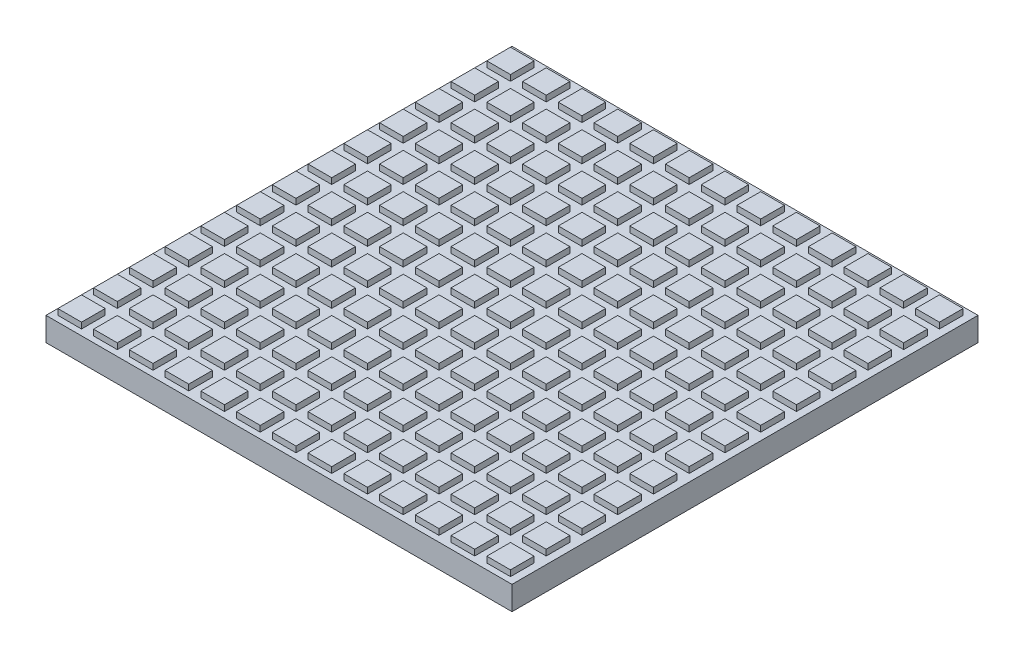
SolidWorks part; units mm, degrees
ref_plane "Front Plane" through (0, 0, 0) normal (0, 0, 1) x (1, 0, 0)
ref_plane "Top Plane" through (0, 0, 0) normal (0, 1, 0) x (1, 0, 0)
ref_plane "Right Plane" through (0, 0, 0) normal (1, 0, 0) x (0, 0, -1)
sketch "Sketch1" plane through (0, 0, 0) normal (0, 1, 0) x (1, 0, 0)
  line L1 (-250, -250) -> (250, -250)
  line L2 (-250, -250) -> (-250, 250)
  line L3 (-250, 250) -> (250, 250)
  line L4 (250, -250) -> (250, 250)
  line L5 (-250, -250) -> (250, 250) construction
  line L6 (-250, 250) -> (250, -250) construction
  point P0 (0, 0)
  dimension "D1" = 500
  dimension "D2" = 500
extrude "Boss-Extrude1" add sketch "Sketch1" along normal blind 25.4
sketch "Sketch2" plane through (0, 25.4, 0) normal (0, 1, 0) x (1, 0, 0)
  line L0 (-250, -250) -> (250, -250) construction
  line L1 (-243.65, -243.65) -> (-218.25, -243.65)
  line L2 (-243.65, -243.65) -> (-243.65, -218.25)
  line L3 (-243.65, -218.25) -> (-218.25, -218.25)
  line L4 (-218.25, -243.65) -> (-218.25, -218.25)
  line L5 (-243.65, -243.65) -> (-218.25, -218.25) construction
  line L6 (-243.65, -218.25) -> (-218.25, -243.65) construction
  line L7 (-250, 250) -> (-250, -250) construction
  line L8 (-205.296, -243.65) -> (-205.296, -218.25)
  line L9 (-205.296, -243.65) -> (-179.896, -243.65)
  line L10 (-179.896, -243.65) -> (-179.896, -218.25)
  line L11 (-205.296, -218.25) -> (-179.896, -218.25)
  line L12 (-166.942, -243.65) -> (-166.942, -218.25)
  line L13 (-166.942, -243.65) -> (-141.542, -243.65)
  line L14 (-141.542, -243.65) -> (-141.542, -218.25)
  line L15 (-166.942, -218.25) -> (-141.542, -218.25)
  line L16 (-128.588, -243.65) -> (-128.588, -218.25)
  line L17 (-128.588, -243.65) -> (-103.188, -243.65)
  line L18 (-103.188, -243.65) -> (-103.188, -218.25)
  line L19 (-128.588, -218.25) -> (-103.188, -218.25)
  line L20 (-90.234, -243.65) -> (-90.234, -218.25)
  line L21 (-90.234, -243.65) -> (-64.834, -243.65)
  line L22 (-64.834, -243.65) -> (-64.834, -218.25)
  line L23 (-90.234, -218.25) -> (-64.834, -218.25)
  line L24 (-51.88, -243.65) -> (-51.88, -218.25)
  line L25 (-51.88, -243.65) -> (-26.48, -243.65)
  line L26 (-26.48, -243.65) -> (-26.48, -218.25)
  line L27 (-51.88, -218.25) -> (-26.48, -218.25)
  line L28 (-13.526, -243.65) -> (-13.526, -218.25)
  line L29 (-13.526, -243.65) -> (11.874, -243.65)
  line L30 (11.874, -243.65) -> (11.874, -218.25)
  line L31 (-13.526, -218.25) -> (11.874, -218.25)
  line L32 (24.828, -243.65) -> (24.828, -218.25)
  line L33 (24.828, -243.65) -> (50.228, -243.65)
  line L34 (50.228, -243.65) -> (50.228, -218.25)
  line L35 (24.828, -218.25) -> (50.228, -218.25)
  line L36 (63.182, -243.65) -> (63.182, -218.25)
  line L37 (63.182, -243.65) -> (88.582, -243.65)
  line L38 (88.582, -243.65) -> (88.582, -218.25)
  line L39 (63.182, -218.25) -> (88.582, -218.25)
  line L40 (101.536, -243.65) -> (101.536, -218.25)
  line L41 (101.536, -243.65) -> (126.936, -243.65)
  line L42 (126.936, -243.65) -> (126.936, -218.25)
  line L43 (101.536, -218.25) -> (126.936, -218.25)
  line L44 (139.89, -243.65) -> (139.89, -218.25)
  line L45 (139.89, -243.65) -> (165.29, -243.65)
  line L46 (165.29, -243.65) -> (165.29, -218.25)
  line L47 (139.89, -218.25) -> (165.29, -218.25)
  line L48 (178.244, -243.65) -> (178.244, -218.25)
  line L49 (178.244, -243.65) -> (203.644, -243.65)
  line L50 (203.644, -243.65) -> (203.644, -218.25)
  line L51 (178.244, -218.25) -> (203.644, -218.25)
  line L52 (216.598, -243.65) -> (216.598, -218.25)
  line L53 (216.598, -243.65) -> (241.998, -243.65)
  line L54 (241.998, -243.65) -> (241.998, -218.25)
  line L55 (216.598, -218.25) -> (241.998, -218.25)
  line L56 (-205.296, -205.296) -> (-205.296, -179.896)
  line L57 (-205.296, -205.296) -> (-179.896, -205.296)
  line L58 (-179.896, -205.296) -> (-179.896, -179.896)
  line L59 (-205.296, -179.896) -> (-179.896, -179.896)
  line L60 (-166.942, -205.296) -> (-166.942, -179.896)
  line L61 (-166.942, -205.296) -> (-141.542, -205.296)
  line L62 (-141.542, -205.296) -> (-141.542, -179.896)
  line L63 (-166.942, -179.896) -> (-141.542, -179.896)
  line L64 (-128.588, -205.296) -> (-128.588, -179.896)
  line L65 (-128.588, -205.296) -> (-103.188, -205.296)
  line L66 (-103.188, -205.296) -> (-103.188, -179.896)
  line L67 (-128.588, -179.896) -> (-103.188, -179.896)
  line L68 (-90.234, -205.296) -> (-90.234, -179.896)
  line L69 (-90.234, -205.296) -> (-64.834, -205.296)
  line L70 (-64.834, -205.296) -> (-64.834, -179.896)
  line L71 (-90.234, -179.896) -> (-64.834, -179.896)
  line L72 (-51.88, -205.296) -> (-51.88, -179.896)
  line L73 (-51.88, -205.296) -> (-26.48, -205.296)
  line L74 (-26.48, -205.296) -> (-26.48, -179.896)
  line L75 (-51.88, -179.896) -> (-26.48, -179.896)
  line L76 (-13.526, -205.296) -> (-13.526, -179.896)
  line L77 (-13.526, -205.296) -> (11.874, -205.296)
  line L78 (11.874, -205.296) -> (11.874, -179.896)
  line L79 (-13.526, -179.896) -> (11.874, -179.896)
  line L80 (24.828, -205.296) -> (24.828, -179.896)
  line L81 (24.828, -205.296) -> (50.228, -205.296)
  line L82 (50.228, -205.296) -> (50.228, -179.896)
  line L83 (24.828, -179.896) -> (50.228, -179.896)
  line L84 (63.182, -205.296) -> (63.182, -179.896)
  line L85 (63.182, -205.296) -> (88.582, -205.296)
  line L86 (88.582, -205.296) -> (88.582, -179.896)
  line L87 (63.182, -179.896) -> (88.582, -179.896)
  line L88 (101.536, -205.296) -> (101.536, -179.896)
  line L89 (101.536, -205.296) -> (126.936, -205.296)
  line L90 (126.936, -205.296) -> (126.936, -179.896)
  line L91 (101.536, -179.896) -> (126.936, -179.896)
  line L92 (139.89, -205.296) -> (139.89, -179.896)
  line L93 (139.89, -205.296) -> (165.29, -205.296)
  line L94 (165.29, -205.296) -> (165.29, -179.896)
  line L95 (139.89, -179.896) -> (165.29, -179.896)
  line L96 (178.244, -205.296) -> (178.244, -179.896)
  line L97 (178.244, -205.296) -> (203.644, -205.296)
  line L98 (203.644, -205.296) -> (203.644, -179.896)
  line L99 (178.244, -179.896) -> (203.644, -179.896)
  line L100 (216.598, -205.296) -> (216.598, -179.896)
  line L101 (216.598, -205.296) -> (241.998, -205.296)
  line L102 (241.998, -205.296) -> (241.998, -179.896)
  line L103 (216.598, -179.896) -> (241.998, -179.896)
  line L104 (-205.296, -166.942) -> (-205.296, -141.542)
  line L105 (-205.296, -166.942) -> (-179.896, -166.942)
  line L106 (-179.896, -166.942) -> (-179.896, -141.542)
  line L107 (-205.296, -141.542) -> (-179.896, -141.542)
  line L108 (-166.942, -166.942) -> (-166.942, -141.542)
  line L109 (-166.942, -166.942) -> (-141.542, -166.942)
  line L110 (-141.542, -166.942) -> (-141.542, -141.542)
  line L111 (-166.942, -141.542) -> (-141.542, -141.542)
  line L112 (-128.588, -166.942) -> (-128.588, -141.542)
  line L113 (-128.588, -166.942) -> (-103.188, -166.942)
  line L114 (-103.188, -166.942) -> (-103.188, -141.542)
  line L115 (-128.588, -141.542) -> (-103.188, -141.542)
  line L116 (-90.234, -166.942) -> (-90.234, -141.542)
  line L117 (-90.234, -166.942) -> (-64.834, -166.942)
  line L118 (-64.834, -166.942) -> (-64.834, -141.542)
  line L119 (-90.234, -141.542) -> (-64.834, -141.542)
  line L120 (-51.88, -166.942) -> (-51.88, -141.542)
  line L121 (-51.88, -166.942) -> (-26.48, -166.942)
  line L122 (-26.48, -166.942) -> (-26.48, -141.542)
  line L123 (-51.88, -141.542) -> (-26.48, -141.542)
  line L124 (-13.526, -166.942) -> (-13.526, -141.542)
  line L125 (-13.526, -166.942) -> (11.874, -166.942)
  line L126 (11.874, -166.942) -> (11.874, -141.542)
  line L127 (-13.526, -141.542) -> (11.874, -141.542)
  line L128 (24.828, -166.942) -> (24.828, -141.542)
  line L129 (24.828, -166.942) -> (50.228, -166.942)
  line L130 (50.228, -166.942) -> (50.228, -141.542)
  line L131 (24.828, -141.542) -> (50.228, -141.542)
  line L132 (63.182, -166.942) -> (63.182, -141.542)
  line L133 (63.182, -166.942) -> (88.582, -166.942)
  line L134 (88.582, -166.942) -> (88.582, -141.542)
  line L135 (63.182, -141.542) -> (88.582, -141.542)
  line L136 (101.536, -166.942) -> (101.536, -141.542)
  line L137 (101.536, -166.942) -> (126.936, -166.942)
  line L138 (126.936, -166.942) -> (126.936, -141.542)
  line L139 (101.536, -141.542) -> (126.936, -141.542)
  line L140 (139.89, -166.942) -> (139.89, -141.542)
  line L141 (139.89, -166.942) -> (165.29, -166.942)
  line L142 (165.29, -166.942) -> (165.29, -141.542)
  line L143 (139.89, -141.542) -> (165.29, -141.542)
  line L144 (178.244, -166.942) -> (178.244, -141.542)
  line L145 (178.244, -166.942) -> (203.644, -166.942)
  line L146 (203.644, -166.942) -> (203.644, -141.542)
  line L147 (178.244, -141.542) -> (203.644, -141.542)
  line L148 (216.598, -166.942) -> (216.598, -141.542)
  line L149 (216.598, -166.942) -> (241.998, -166.942)
  line L150 (241.998, -166.942) -> (241.998, -141.542)
  line L151 (216.598, -141.542) -> (241.998, -141.542)
  line L152 (-205.296, -128.588) -> (-205.296, -103.188)
  line L153 (-205.296, -128.588) -> (-179.896, -128.588)
  line L154 (-179.896, -128.588) -> (-179.896, -103.188)
  line L155 (-205.296, -103.188) -> (-179.896, -103.188)
  line L156 (-166.942, -128.588) -> (-166.942, -103.188)
  line L157 (-166.942, -128.588) -> (-141.542, -128.588)
  line L158 (-141.542, -128.588) -> (-141.542, -103.188)
  line L159 (-166.942, -103.188) -> (-141.542, -103.188)
  line L160 (-128.588, -128.588) -> (-128.588, -103.188)
  line L161 (-128.588, -128.588) -> (-103.188, -128.588)
  line L162 (-103.188, -128.588) -> (-103.188, -103.188)
  line L163 (-128.588, -103.188) -> (-103.188, -103.188)
  line L164 (-90.234, -128.588) -> (-90.234, -103.188)
  line L165 (-90.234, -128.588) -> (-64.834, -128.588)
  line L166 (-64.834, -128.588) -> (-64.834, -103.188)
  line L167 (-90.234, -103.188) -> (-64.834, -103.188)
  line L168 (-51.88, -128.588) -> (-51.88, -103.188)
  line L169 (-51.88, -128.588) -> (-26.48, -128.588)
  line L170 (-26.48, -128.588) -> (-26.48, -103.188)
  line L171 (-51.88, -103.188) -> (-26.48, -103.188)
  line L172 (-13.526, -128.588) -> (-13.526, -103.188)
  line L173 (-13.526, -128.588) -> (11.874, -128.588)
  line L174 (11.874, -128.588) -> (11.874, -103.188)
  line L175 (-13.526, -103.188) -> (11.874, -103.188)
  line L176 (24.828, -128.588) -> (24.828, -103.188)
  line L177 (24.828, -128.588) -> (50.228, -128.588)
  line L178 (50.228, -128.588) -> (50.228, -103.188)
  line L179 (24.828, -103.188) -> (50.228, -103.188)
  line L180 (63.182, -128.588) -> (63.182, -103.188)
  line L181 (63.182, -128.588) -> (88.582, -128.588)
  line L182 (88.582, -128.588) -> (88.582, -103.188)
  line L183 (63.182, -103.188) -> (88.582, -103.188)
  line L184 (101.536, -128.588) -> (101.536, -103.188)
  line L185 (101.536, -128.588) -> (126.936, -128.588)
  line L186 (126.936, -128.588) -> (126.936, -103.188)
  line L187 (101.536, -103.188) -> (126.936, -103.188)
  line L188 (139.89, -128.588) -> (139.89, -103.188)
  line L189 (139.89, -128.588) -> (165.29, -128.588)
  line L190 (165.29, -128.588) -> (165.29, -103.188)
  line L191 (139.89, -103.188) -> (165.29, -103.188)
  line L192 (178.244, -128.588) -> (178.244, -103.188)
  line L193 (178.244, -128.588) -> (203.644, -128.588)
  line L194 (203.644, -128.588) -> (203.644, -103.188)
  line L195 (178.244, -103.188) -> (203.644, -103.188)
  line L196 (216.598, -128.588) -> (216.598, -103.188)
  line L197 (216.598, -128.588) -> (241.998, -128.588)
  line L198 (241.998, -128.588) -> (241.998, -103.188)
  line L199 (216.598, -103.188) -> (241.998, -103.188)
  line L200 (-205.296, -90.234) -> (-205.296, -64.834)
  line L201 (-205.296, -90.234) -> (-179.896, -90.234)
  line L202 (-179.896, -90.234) -> (-179.896, -64.834)
  line L203 (-205.296, -64.834) -> (-179.896, -64.834)
  line L204 (-166.942, -90.234) -> (-166.942, -64.834)
  line L205 (-166.942, -90.234) -> (-141.542, -90.234)
  line L206 (-141.542, -90.234) -> (-141.542, -64.834)
  line L207 (-166.942, -64.834) -> (-141.542, -64.834)
  line L208 (-128.588, -90.234) -> (-128.588, -64.834)
  line L209 (-128.588, -90.234) -> (-103.188, -90.234)
  line L210 (-103.188, -90.234) -> (-103.188, -64.834)
  line L211 (-128.588, -64.834) -> (-103.188, -64.834)
  line L212 (-90.234, -90.234) -> (-90.234, -64.834)
  line L213 (-90.234, -90.234) -> (-64.834, -90.234)
  line L214 (-64.834, -90.234) -> (-64.834, -64.834)
  line L215 (-90.234, -64.834) -> (-64.834, -64.834)
  line L216 (-51.88, -90.234) -> (-51.88, -64.834)
  line L217 (-51.88, -90.234) -> (-26.48, -90.234)
  line L218 (-26.48, -90.234) -> (-26.48, -64.834)
  line L219 (-51.88, -64.834) -> (-26.48, -64.834)
  line L220 (-13.526, -90.234) -> (-13.526, -64.834)
  line L221 (-13.526, -90.234) -> (11.874, -90.234)
  line L222 (11.874, -90.234) -> (11.874, -64.834)
  line L223 (-13.526, -64.834) -> (11.874, -64.834)
  line L224 (24.828, -90.234) -> (24.828, -64.834)
  line L225 (24.828, -90.234) -> (50.228, -90.234)
  line L226 (50.228, -90.234) -> (50.228, -64.834)
  line L227 (24.828, -64.834) -> (50.228, -64.834)
  line L228 (63.182, -90.234) -> (63.182, -64.834)
  line L229 (63.182, -90.234) -> (88.582, -90.234)
  line L230 (88.582, -90.234) -> (88.582, -64.834)
  line L231 (63.182, -64.834) -> (88.582, -64.834)
  line L232 (101.536, -90.234) -> (101.536, -64.834)
  line L233 (101.536, -90.234) -> (126.936, -90.234)
  line L234 (126.936, -90.234) -> (126.936, -64.834)
  line L235 (101.536, -64.834) -> (126.936, -64.834)
  line L236 (139.89, -90.234) -> (139.89, -64.834)
  line L237 (139.89, -90.234) -> (165.29, -90.234)
  line L238 (165.29, -90.234) -> (165.29, -64.834)
  line L239 (139.89, -64.834) -> (165.29, -64.834)
  line L240 (178.244, -90.234) -> (178.244, -64.834)
  line L241 (178.244, -90.234) -> (203.644, -90.234)
  line L242 (203.644, -90.234) -> (203.644, -64.834)
  line L243 (178.244, -64.834) -> (203.644, -64.834)
  line L244 (216.598, -90.234) -> (216.598, -64.834)
  line L245 (216.598, -90.234) -> (241.998, -90.234)
  line L246 (241.998, -90.234) -> (241.998, -64.834)
  line L247 (216.598, -64.834) -> (241.998, -64.834)
  line L248 (-205.296, -51.88) -> (-205.296, -26.48)
  line L249 (-205.296, -51.88) -> (-179.896, -51.88)
  line L250 (-179.896, -51.88) -> (-179.896, -26.48)
  line L251 (-205.296, -26.48) -> (-179.896, -26.48)
  line L252 (-166.942, -51.88) -> (-166.942, -26.48)
  line L253 (-166.942, -51.88) -> (-141.542, -51.88)
  line L254 (-141.542, -51.88) -> (-141.542, -26.48)
  line L255 (-166.942, -26.48) -> (-141.542, -26.48)
  line L256 (-128.588, -51.88) -> (-128.588, -26.48)
  line L257 (-128.588, -51.88) -> (-103.188, -51.88)
  line L258 (-103.188, -51.88) -> (-103.188, -26.48)
  line L259 (-128.588, -26.48) -> (-103.188, -26.48)
  line L260 (-90.234, -51.88) -> (-90.234, -26.48)
  line L261 (-90.234, -51.88) -> (-64.834, -51.88)
  line L262 (-64.834, -51.88) -> (-64.834, -26.48)
  line L263 (-90.234, -26.48) -> (-64.834, -26.48)
  line L264 (-51.88, -51.88) -> (-51.88, -26.48)
  line L265 (-51.88, -51.88) -> (-26.48, -51.88)
  line L266 (-26.48, -51.88) -> (-26.48, -26.48)
  line L267 (-51.88, -26.48) -> (-26.48, -26.48)
  line L268 (-13.526, -51.88) -> (-13.526, -26.48)
  line L269 (-13.526, -51.88) -> (11.874, -51.88)
  line L270 (11.874, -51.88) -> (11.874, -26.48)
  line L271 (-13.526, -26.48) -> (11.874, -26.48)
  line L272 (24.828, -51.88) -> (24.828, -26.48)
  line L273 (24.828, -51.88) -> (50.228, -51.88)
  line L274 (50.228, -51.88) -> (50.228, -26.48)
  line L275 (24.828, -26.48) -> (50.228, -26.48)
  line L276 (63.182, -51.88) -> (63.182, -26.48)
  line L277 (63.182, -51.88) -> (88.582, -51.88)
  line L278 (88.582, -51.88) -> (88.582, -26.48)
  line L279 (63.182, -26.48) -> (88.582, -26.48)
  line L280 (101.536, -51.88) -> (101.536, -26.48)
  line L281 (101.536, -51.88) -> (126.936, -51.88)
  line L282 (126.936, -51.88) -> (126.936, -26.48)
  line L283 (101.536, -26.48) -> (126.936, -26.48)
  line L284 (139.89, -51.88) -> (139.89, -26.48)
  line L285 (139.89, -51.88) -> (165.29, -51.88)
  line L286 (165.29, -51.88) -> (165.29, -26.48)
  line L287 (139.89, -26.48) -> (165.29, -26.48)
  line L288 (178.244, -51.88) -> (178.244, -26.48)
  line L289 (178.244, -51.88) -> (203.644, -51.88)
  line L290 (203.644, -51.88) -> (203.644, -26.48)
  line L291 (178.244, -26.48) -> (203.644, -26.48)
  line L292 (216.598, -51.88) -> (216.598, -26.48)
  line L293 (216.598, -51.88) -> (241.998, -51.88)
  line L294 (241.998, -51.88) -> (241.998, -26.48)
  line L295 (216.598, -26.48) -> (241.998, -26.48)
  line L296 (-205.296, -13.526) -> (-205.296, 11.874)
  line L297 (-205.296, -13.526) -> (-179.896, -13.526)
  line L298 (-179.896, -13.526) -> (-179.896, 11.874)
  line L299 (-205.296, 11.874) -> (-179.896, 11.874)
  line L300 (-166.942, -13.526) -> (-166.942, 11.874)
  line L301 (-166.942, -13.526) -> (-141.542, -13.526)
  line L302 (-141.542, -13.526) -> (-141.542, 11.874)
  line L303 (-166.942, 11.874) -> (-141.542, 11.874)
  line L304 (-128.588, -13.526) -> (-128.588, 11.874)
  line L305 (-128.588, -13.526) -> (-103.188, -13.526)
  line L306 (-103.188, -13.526) -> (-103.188, 11.874)
  line L307 (-128.588, 11.874) -> (-103.188, 11.874)
  line L308 (-90.234, -13.526) -> (-90.234, 11.874)
  line L309 (-90.234, -13.526) -> (-64.834, -13.526)
  line L310 (-64.834, -13.526) -> (-64.834, 11.874)
  line L311 (-90.234, 11.874) -> (-64.834, 11.874)
  line L312 (-51.88, -13.526) -> (-51.88, 11.874)
  line L313 (-51.88, -13.526) -> (-26.48, -13.526)
  line L314 (-26.48, -13.526) -> (-26.48, 11.874)
  line L315 (-51.88, 11.874) -> (-26.48, 11.874)
  line L316 (-13.526, -13.526) -> (-13.526, 11.874)
  line L317 (-13.526, -13.526) -> (11.874, -13.526)
  line L318 (11.874, -13.526) -> (11.874, 11.874)
  line L319 (-13.526, 11.874) -> (11.874, 11.874)
  line L320 (24.828, -13.526) -> (24.828, 11.874)
  line L321 (24.828, -13.526) -> (50.228, -13.526)
  line L322 (50.228, -13.526) -> (50.228, 11.874)
  line L323 (24.828, 11.874) -> (50.228, 11.874)
  line L324 (63.182, -13.526) -> (63.182, 11.874)
  line L325 (63.182, -13.526) -> (88.582, -13.526)
  line L326 (88.582, -13.526) -> (88.582, 11.874)
  line L327 (63.182, 11.874) -> (88.582, 11.874)
  line L328 (101.536, -13.526) -> (101.536, 11.874)
  line L329 (101.536, -13.526) -> (126.936, -13.526)
  line L330 (126.936, -13.526) -> (126.936, 11.874)
  line L331 (101.536, 11.874) -> (126.936, 11.874)
  line L332 (139.89, -13.526) -> (139.89, 11.874)
  line L333 (139.89, -13.526) -> (165.29, -13.526)
  line L334 (165.29, -13.526) -> (165.29, 11.874)
  line L335 (139.89, 11.874) -> (165.29, 11.874)
  line L336 (178.244, -13.526) -> (178.244, 11.874)
  line L337 (178.244, -13.526) -> (203.644, -13.526)
  line L338 (203.644, -13.526) -> (203.644, 11.874)
  line L339 (178.244, 11.874) -> (203.644, 11.874)
  line L340 (216.598, -13.526) -> (216.598, 11.874)
  line L341 (216.598, -13.526) -> (241.998, -13.526)
  line L342 (241.998, -13.526) -> (241.998, 11.874)
  line L343 (216.598, 11.874) -> (241.998, 11.874)
  line L344 (-205.296, 24.828) -> (-205.296, 50.228)
  line L345 (-205.296, 24.828) -> (-179.896, 24.828)
  line L346 (-179.896, 24.828) -> (-179.896, 50.228)
  line L347 (-205.296, 50.228) -> (-179.896, 50.228)
  line L348 (-166.942, 24.828) -> (-166.942, 50.228)
  line L349 (-166.942, 24.828) -> (-141.542, 24.828)
  line L350 (-141.542, 24.828) -> (-141.542, 50.228)
  line L351 (-166.942, 50.228) -> (-141.542, 50.228)
  line L352 (-128.588, 24.828) -> (-128.588, 50.228)
  line L353 (-128.588, 24.828) -> (-103.188, 24.828)
  line L354 (-103.188, 24.828) -> (-103.188, 50.228)
  line L355 (-128.588, 50.228) -> (-103.188, 50.228)
  line L356 (-90.234, 24.828) -> (-90.234, 50.228)
  line L357 (-90.234, 24.828) -> (-64.834, 24.828)
  line L358 (-64.834, 24.828) -> (-64.834, 50.228)
  line L359 (-90.234, 50.228) -> (-64.834, 50.228)
  line L360 (-51.88, 24.828) -> (-51.88, 50.228)
  line L361 (-51.88, 24.828) -> (-26.48, 24.828)
  line L362 (-26.48, 24.828) -> (-26.48, 50.228)
  line L363 (-51.88, 50.228) -> (-26.48, 50.228)
  line L364 (-13.526, 24.828) -> (-13.526, 50.228)
  line L365 (-13.526, 24.828) -> (11.874, 24.828)
  line L366 (11.874, 24.828) -> (11.874, 50.228)
  line L367 (-13.526, 50.228) -> (11.874, 50.228)
  line L368 (24.828, 24.828) -> (24.828, 50.228)
  line L369 (24.828, 24.828) -> (50.228, 24.828)
  line L370 (50.228, 24.828) -> (50.228, 50.228)
  line L371 (24.828, 50.228) -> (50.228, 50.228)
  line L372 (63.182, 24.828) -> (63.182, 50.228)
  line L373 (63.182, 24.828) -> (88.582, 24.828)
  line L374 (88.582, 24.828) -> (88.582, 50.228)
  line L375 (63.182, 50.228) -> (88.582, 50.228)
  line L376 (101.536, 24.828) -> (101.536, 50.228)
  line L377 (101.536, 24.828) -> (126.936, 24.828)
  line L378 (126.936, 24.828) -> (126.936, 50.228)
  line L379 (101.536, 50.228) -> (126.936, 50.228)
  line L380 (139.89, 24.828) -> (139.89, 50.228)
  line L381 (139.89, 24.828) -> (165.29, 24.828)
  line L382 (165.29, 24.828) -> (165.29, 50.228)
  line L383 (139.89, 50.228) -> (165.29, 50.228)
  line L384 (178.244, 24.828) -> (178.244, 50.228)
  line L385 (178.244, 24.828) -> (203.644, 24.828)
  line L386 (203.644, 24.828) -> (203.644, 50.228)
  line L387 (178.244, 50.228) -> (203.644, 50.228)
  line L388 (216.598, 24.828) -> (216.598, 50.228)
  line L389 (216.598, 24.828) -> (241.998, 24.828)
  line L390 (241.998, 24.828) -> (241.998, 50.228)
  line L391 (216.598, 50.228) -> (241.998, 50.228)
  line L392 (-205.296, 63.182) -> (-205.296, 88.582)
  line L393 (-205.296, 63.182) -> (-179.896, 63.182)
  line L394 (-179.896, 63.182) -> (-179.896, 88.582)
  line L395 (-205.296, 88.582) -> (-179.896, 88.582)
  line L396 (-166.942, 63.182) -> (-166.942, 88.582)
  line L397 (-166.942, 63.182) -> (-141.542, 63.182)
  line L398 (-141.542, 63.182) -> (-141.542, 88.582)
  line L399 (-166.942, 88.582) -> (-141.542, 88.582)
  line L400 (-128.588, 63.182) -> (-128.588, 88.582)
  line L401 (-128.588, 63.182) -> (-103.188, 63.182)
  line L402 (-103.188, 63.182) -> (-103.188, 88.582)
  line L403 (-128.588, 88.582) -> (-103.188, 88.582)
  line L404 (-90.234, 63.182) -> (-90.234, 88.582)
  line L405 (-90.234, 63.182) -> (-64.834, 63.182)
  line L406 (-64.834, 63.182) -> (-64.834, 88.582)
  line L407 (-90.234, 88.582) -> (-64.834, 88.582)
  line L408 (-51.88, 63.182) -> (-51.88, 88.582)
  line L409 (-51.88, 63.182) -> (-26.48, 63.182)
  line L410 (-26.48, 63.182) -> (-26.48, 88.582)
  line L411 (-51.88, 88.582) -> (-26.48, 88.582)
  line L412 (-13.526, 63.182) -> (-13.526, 88.582)
  line L413 (-13.526, 63.182) -> (11.874, 63.182)
  line L414 (11.874, 63.182) -> (11.874, 88.582)
  line L415 (-13.526, 88.582) -> (11.874, 88.582)
  line L416 (24.828, 63.182) -> (24.828, 88.582)
  line L417 (24.828, 63.182) -> (50.228, 63.182)
  line L418 (50.228, 63.182) -> (50.228, 88.582)
  line L419 (24.828, 88.582) -> (50.228, 88.582)
  line L420 (63.182, 63.182) -> (63.182, 88.582)
  line L421 (63.182, 63.182) -> (88.582, 63.182)
  line L422 (88.582, 63.182) -> (88.582, 88.582)
  line L423 (63.182, 88.582) -> (88.582, 88.582)
  line L424 (101.536, 63.182) -> (101.536, 88.582)
  line L425 (101.536, 63.182) -> (126.936, 63.182)
  line L426 (126.936, 63.182) -> (126.936, 88.582)
  line L427 (101.536, 88.582) -> (126.936, 88.582)
  line L428 (139.89, 63.182) -> (139.89, 88.582)
  line L429 (139.89, 63.182) -> (165.29, 63.182)
  line L430 (165.29, 63.182) -> (165.29, 88.582)
  line L431 (139.89, 88.582) -> (165.29, 88.582)
  line L432 (178.244, 63.182) -> (178.244, 88.582)
  line L433 (178.244, 63.182) -> (203.644, 63.182)
  line L434 (203.644, 63.182) -> (203.644, 88.582)
  line L435 (178.244, 88.582) -> (203.644, 88.582)
  line L436 (216.598, 63.182) -> (216.598, 88.582)
  line L437 (216.598, 63.182) -> (241.998, 63.182)
  line L438 (241.998, 63.182) -> (241.998, 88.582)
  line L439 (216.598, 88.582) -> (241.998, 88.582)
  line L440 (-205.296, 101.536) -> (-205.296, 126.936)
  line L441 (-205.296, 101.536) -> (-179.896, 101.536)
  line L442 (-179.896, 101.536) -> (-179.896, 126.936)
  line L443 (-205.296, 126.936) -> (-179.896, 126.936)
  line L444 (-166.942, 101.536) -> (-166.942, 126.936)
  line L445 (-166.942, 101.536) -> (-141.542, 101.536)
  line L446 (-141.542, 101.536) -> (-141.542, 126.936)
  line L447 (-166.942, 126.936) -> (-141.542, 126.936)
  line L448 (-128.588, 101.536) -> (-128.588, 126.936)
  line L449 (-128.588, 101.536) -> (-103.188, 101.536)
  line L450 (-103.188, 101.536) -> (-103.188, 126.936)
  line L451 (-128.588, 126.936) -> (-103.188, 126.936)
  line L452 (-90.234, 101.536) -> (-90.234, 126.936)
  line L453 (-90.234, 101.536) -> (-64.834, 101.536)
  line L454 (-64.834, 101.536) -> (-64.834, 126.936)
  line L455 (-90.234, 126.936) -> (-64.834, 126.936)
  line L456 (-51.88, 101.536) -> (-51.88, 126.936)
  line L457 (-51.88, 101.536) -> (-26.48, 101.536)
  line L458 (-26.48, 101.536) -> (-26.48, 126.936)
  line L459 (-51.88, 126.936) -> (-26.48, 126.936)
  line L460 (-13.526, 101.536) -> (-13.526, 126.936)
  line L461 (-13.526, 101.536) -> (11.874, 101.536)
  line L462 (11.874, 101.536) -> (11.874, 126.936)
  line L463 (-13.526, 126.936) -> (11.874, 126.936)
  line L464 (24.828, 101.536) -> (24.828, 126.936)
  line L465 (24.828, 101.536) -> (50.228, 101.536)
  line L466 (50.228, 101.536) -> (50.228, 126.936)
  line L467 (24.828, 126.936) -> (50.228, 126.936)
  line L468 (63.182, 101.536) -> (63.182, 126.936)
  line L469 (63.182, 101.536) -> (88.582, 101.536)
  line L470 (88.582, 101.536) -> (88.582, 126.936)
  line L471 (63.182, 126.936) -> (88.582, 126.936)
  line L472 (101.536, 101.536) -> (101.536, 126.936)
  line L473 (101.536, 101.536) -> (126.936, 101.536)
  line L474 (126.936, 101.536) -> (126.936, 126.936)
  line L475 (101.536, 126.936) -> (126.936, 126.936)
  line L476 (139.89, 101.536) -> (139.89, 126.936)
  line L477 (139.89, 101.536) -> (165.29, 101.536)
  line L478 (165.29, 101.536) -> (165.29, 126.936)
  line L479 (139.89, 126.936) -> (165.29, 126.936)
  line L480 (178.244, 101.536) -> (178.244, 126.936)
  line L481 (178.244, 101.536) -> (203.644, 101.536)
  line L482 (203.644, 101.536) -> (203.644, 126.936)
  line L483 (178.244, 126.936) -> (203.644, 126.936)
  line L484 (216.598, 101.536) -> (216.598, 126.936)
  line L485 (216.598, 101.536) -> (241.998, 101.536)
  line L486 (241.998, 101.536) -> (241.998, 126.936)
  line L487 (216.598, 126.936) -> (241.998, 126.936)
  line L488 (-205.296, 139.89) -> (-205.296, 165.29)
  line L489 (-205.296, 139.89) -> (-179.896, 139.89)
  line L490 (-179.896, 139.89) -> (-179.896, 165.29)
  line L491 (-205.296, 165.29) -> (-179.896, 165.29)
  line L492 (-166.942, 139.89) -> (-166.942, 165.29)
  line L493 (-166.942, 139.89) -> (-141.542, 139.89)
  line L494 (-141.542, 139.89) -> (-141.542, 165.29)
  line L495 (-166.942, 165.29) -> (-141.542, 165.29)
  line L496 (-128.588, 139.89) -> (-128.588, 165.29)
  line L497 (-128.588, 139.89) -> (-103.188, 139.89)
  line L498 (-103.188, 139.89) -> (-103.188, 165.29)
  line L499 (-128.588, 165.29) -> (-103.188, 165.29)
  line L500 (-90.234, 139.89) -> (-90.234, 165.29)
  line L501 (-90.234, 139.89) -> (-64.834, 139.89)
  line L502 (-64.834, 139.89) -> (-64.834, 165.29)
  line L503 (-90.234, 165.29) -> (-64.834, 165.29)
  line L504 (-51.88, 139.89) -> (-51.88, 165.29)
  line L505 (-51.88, 139.89) -> (-26.48, 139.89)
  line L506 (-26.48, 139.89) -> (-26.48, 165.29)
  line L507 (-51.88, 165.29) -> (-26.48, 165.29)
  line L508 (-13.526, 139.89) -> (-13.526, 165.29)
  line L509 (-13.526, 139.89) -> (11.874, 139.89)
  line L510 (11.874, 139.89) -> (11.874, 165.29)
  line L511 (-13.526, 165.29) -> (11.874, 165.29)
  line L512 (24.828, 139.89) -> (24.828, 165.29)
  line L513 (24.828, 139.89) -> (50.228, 139.89)
  line L514 (50.228, 139.89) -> (50.228, 165.29)
  line L515 (24.828, 165.29) -> (50.228, 165.29)
  line L516 (63.182, 139.89) -> (63.182, 165.29)
  line L517 (63.182, 139.89) -> (88.582, 139.89)
  line L518 (88.582, 139.89) -> (88.582, 165.29)
  line L519 (63.182, 165.29) -> (88.582, 165.29)
  line L520 (101.536, 139.89) -> (101.536, 165.29)
  line L521 (101.536, 139.89) -> (126.936, 139.89)
  line L522 (126.936, 139.89) -> (126.936, 165.29)
  line L523 (101.536, 165.29) -> (126.936, 165.29)
  line L524 (139.89, 139.89) -> (139.89, 165.29)
  line L525 (139.89, 139.89) -> (165.29, 139.89)
  line L526 (165.29, 139.89) -> (165.29, 165.29)
  line L527 (139.89, 165.29) -> (165.29, 165.29)
  line L528 (178.244, 139.89) -> (178.244, 165.29)
  line L529 (178.244, 139.89) -> (203.644, 139.89)
  line L530 (203.644, 139.89) -> (203.644, 165.29)
  line L531 (178.244, 165.29) -> (203.644, 165.29)
  line L532 (216.598, 139.89) -> (216.598, 165.29)
  line L533 (216.598, 139.89) -> (241.998, 139.89)
  line L534 (241.998, 139.89) -> (241.998, 165.29)
  line L535 (216.598, 165.29) -> (241.998, 165.29)
  line L536 (-205.296, 178.244) -> (-205.296, 203.644)
  line L537 (-205.296, 178.244) -> (-179.896, 178.244)
  line L538 (-179.896, 178.244) -> (-179.896, 203.644)
  line L539 (-205.296, 203.644) -> (-179.896, 203.644)
  line L540 (-166.942, 178.244) -> (-166.942, 203.644)
  line L541 (-166.942, 178.244) -> (-141.542, 178.244)
  line L542 (-141.542, 178.244) -> (-141.542, 203.644)
  line L543 (-166.942, 203.644) -> (-141.542, 203.644)
  line L544 (-128.588, 178.244) -> (-128.588, 203.644)
  line L545 (-128.588, 178.244) -> (-103.188, 178.244)
  line L546 (-103.188, 178.244) -> (-103.188, 203.644)
  line L547 (-128.588, 203.644) -> (-103.188, 203.644)
  line L548 (-90.234, 178.244) -> (-90.234, 203.644)
  line L549 (-90.234, 178.244) -> (-64.834, 178.244)
  line L550 (-64.834, 178.244) -> (-64.834, 203.644)
  line L551 (-90.234, 203.644) -> (-64.834, 203.644)
  line L552 (-51.88, 178.244) -> (-51.88, 203.644)
  line L553 (-51.88, 178.244) -> (-26.48, 178.244)
  line L554 (-26.48, 178.244) -> (-26.48, 203.644)
  line L555 (-51.88, 203.644) -> (-26.48, 203.644)
  line L556 (-13.526, 178.244) -> (-13.526, 203.644)
  line L557 (-13.526, 178.244) -> (11.874, 178.244)
  line L558 (11.874, 178.244) -> (11.874, 203.644)
  line L559 (-13.526, 203.644) -> (11.874, 203.644)
  line L560 (24.828, 178.244) -> (24.828, 203.644)
  line L561 (24.828, 178.244) -> (50.228, 178.244)
  line L562 (50.228, 178.244) -> (50.228, 203.644)
  line L563 (24.828, 203.644) -> (50.228, 203.644)
  line L564 (63.182, 178.244) -> (63.182, 203.644)
  line L565 (63.182, 178.244) -> (88.582, 178.244)
  line L566 (88.582, 178.244) -> (88.582, 203.644)
  line L567 (63.182, 203.644) -> (88.582, 203.644)
  line L568 (101.536, 178.244) -> (101.536, 203.644)
  line L569 (101.536, 178.244) -> (126.936, 178.244)
  line L570 (126.936, 178.244) -> (126.936, 203.644)
  line L571 (101.536, 203.644) -> (126.936, 203.644)
  line L572 (139.89, 178.244) -> (139.89, 203.644)
  line L573 (139.89, 178.244) -> (165.29, 178.244)
  line L574 (165.29, 178.244) -> (165.29, 203.644)
  line L575 (139.89, 203.644) -> (165.29, 203.644)
  line L576 (178.244, 178.244) -> (178.244, 203.644)
  line L577 (178.244, 178.244) -> (203.644, 178.244)
  line L578 (203.644, 178.244) -> (203.644, 203.644)
  line L579 (178.244, 203.644) -> (203.644, 203.644)
  line L580 (216.598, 178.244) -> (216.598, 203.644)
  line L581 (216.598, 178.244) -> (241.998, 178.244)
  line L582 (241.998, 178.244) -> (241.998, 203.644)
  line L583 (216.598, 203.644) -> (241.998, 203.644)
  line L584 (-205.296, 216.598) -> (-205.296, 241.998)
  line L585 (-205.296, 216.598) -> (-179.896, 216.598)
  line L586 (-179.896, 216.598) -> (-179.896, 241.998)
  line L587 (-205.296, 241.998) -> (-179.896, 241.998)
  line L588 (-166.942, 216.598) -> (-166.942, 241.998)
  line L589 (-166.942, 216.598) -> (-141.542, 216.598)
  line L590 (-141.542, 216.598) -> (-141.542, 241.998)
  line L591 (-166.942, 241.998) -> (-141.542, 241.998)
  line L592 (-128.588, 216.598) -> (-128.588, 241.998)
  line L593 (-128.588, 216.598) -> (-103.188, 216.598)
  line L594 (-103.188, 216.598) -> (-103.188, 241.998)
  line L595 (-128.588, 241.998) -> (-103.188, 241.998)
  line L596 (-90.234, 216.598) -> (-90.234, 241.998)
  line L597 (-90.234, 216.598) -> (-64.834, 216.598)
  line L598 (-64.834, 216.598) -> (-64.834, 241.998)
  line L599 (-90.234, 241.998) -> (-64.834, 241.998)
  line L600 (-51.88, 216.598) -> (-51.88, 241.998)
  line L601 (-51.88, 216.598) -> (-26.48, 216.598)
  line L602 (-26.48, 216.598) -> (-26.48, 241.998)
  line L603 (-51.88, 241.998) -> (-26.48, 241.998)
  line L604 (-13.526, 216.598) -> (-13.526, 241.998)
  line L605 (-13.526, 216.598) -> (11.874, 216.598)
  line L606 (11.874, 216.598) -> (11.874, 241.998)
  line L607 (-13.526, 241.998) -> (11.874, 241.998)
  line L608 (24.828, 216.598) -> (24.828, 241.998)
  line L609 (24.828, 216.598) -> (50.228, 216.598)
  line L610 (50.228, 216.598) -> (50.228, 241.998)
  line L611 (24.828, 241.998) -> (50.228, 241.998)
  line L612 (63.182, 216.598) -> (63.182, 241.998)
  line L613 (63.182, 216.598) -> (88.582, 216.598)
  line L614 (88.582, 216.598) -> (88.582, 241.998)
  line L615 (63.182, 241.998) -> (88.582, 241.998)
  line L616 (101.536, 216.598) -> (101.536, 241.998)
  line L617 (101.536, 216.598) -> (126.936, 216.598)
  line L618 (126.936, 216.598) -> (126.936, 241.998)
  line L619 (101.536, 241.998) -> (126.936, 241.998)
  line L620 (139.89, 216.598) -> (139.89, 241.998)
  line L621 (139.89, 216.598) -> (165.29, 216.598)
  line L622 (165.29, 216.598) -> (165.29, 241.998)
  line L623 (139.89, 241.998) -> (165.29, 241.998)
  line L624 (178.244, 216.598) -> (178.244, 241.998)
  line L625 (178.244, 216.598) -> (203.644, 216.598)
  line L626 (203.644, 216.598) -> (203.644, 241.998)
  line L627 (178.244, 241.998) -> (203.644, 241.998)
  line L628 (216.598, 216.598) -> (216.598, 241.998)
  line L629 (216.598, 216.598) -> (241.998, 216.598)
  line L630 (241.998, 216.598) -> (241.998, 241.998)
  line L631 (216.598, 241.998) -> (241.998, 241.998)
  line L632 (-243.65, -205.296) -> (-243.65, -179.896)
  line L633 (-243.65, -205.296) -> (-218.25, -205.296)
  line L634 (-218.25, -205.296) -> (-218.25, -179.896)
  line L635 (-243.65, -179.896) -> (-218.25, -179.896)
  line L636 (-243.65, -166.942) -> (-243.65, -141.542)
  line L637 (-243.65, -166.942) -> (-218.25, -166.942)
  line L638 (-218.25, -166.942) -> (-218.25, -141.542)
  line L639 (-243.65, -141.542) -> (-218.25, -141.542)
  line L640 (-243.65, -128.588) -> (-243.65, -103.188)
  line L641 (-243.65, -128.588) -> (-218.25, -128.588)
  line L642 (-218.25, -128.588) -> (-218.25, -103.188)
  line L643 (-243.65, -103.188) -> (-218.25, -103.188)
  line L644 (-243.65, -90.234) -> (-243.65, -64.834)
  line L645 (-243.65, -90.234) -> (-218.25, -90.234)
  line L646 (-218.25, -90.234) -> (-218.25, -64.834)
  line L647 (-243.65, -64.834) -> (-218.25, -64.834)
  line L648 (-243.65, -51.88) -> (-243.65, -26.48)
  line L649 (-243.65, -51.88) -> (-218.25, -51.88)
  line L650 (-218.25, -51.88) -> (-218.25, -26.48)
  line L651 (-243.65, -26.48) -> (-218.25, -26.48)
  line L652 (-243.65, -13.526) -> (-243.65, 11.874)
  line L653 (-243.65, -13.526) -> (-218.25, -13.526)
  line L654 (-218.25, -13.526) -> (-218.25, 11.874)
  line L655 (-243.65, 11.874) -> (-218.25, 11.874)
  line L656 (-243.65, 24.828) -> (-243.65, 50.228)
  line L657 (-243.65, 24.828) -> (-218.25, 24.828)
  line L658 (-218.25, 24.828) -> (-218.25, 50.228)
  line L659 (-243.65, 50.228) -> (-218.25, 50.228)
  line L660 (-243.65, 63.182) -> (-243.65, 88.582)
  line L661 (-243.65, 63.182) -> (-218.25, 63.182)
  line L662 (-218.25, 63.182) -> (-218.25, 88.582)
  line L663 (-243.65, 88.582) -> (-218.25, 88.582)
  line L664 (-243.65, 101.536) -> (-243.65, 126.936)
  line L665 (-243.65, 101.536) -> (-218.25, 101.536)
  line L666 (-218.25, 101.536) -> (-218.25, 126.936)
  line L667 (-243.65, 126.936) -> (-218.25, 126.936)
  line L668 (-243.65, 139.89) -> (-243.65, 165.29)
  line L669 (-243.65, 139.89) -> (-218.25, 139.89)
  line L670 (-218.25, 139.89) -> (-218.25, 165.29)
  line L671 (-243.65, 165.29) -> (-218.25, 165.29)
  line L672 (-243.65, 178.244) -> (-243.65, 203.644)
  line L673 (-243.65, 178.244) -> (-218.25, 178.244)
  line L674 (-218.25, 178.244) -> (-218.25, 203.644)
  line L675 (-243.65, 203.644) -> (-218.25, 203.644)
  line L676 (-243.65, 216.598) -> (-243.65, 241.998)
  line L677 (-243.65, 216.598) -> (-218.25, 216.598)
  line L678 (-218.25, 216.598) -> (-218.25, 241.998)
  line L679 (-243.65, 241.998) -> (-218.25, 241.998)
  point P0 (-230.95, -230.95)
  dimension "D1" = 25.4
  dimension "D2" = 25.4
  dimension "D3" = 6.35
  dimension "D4" = 6.35
  dimension "D5" = 13
  dimension "D6" = 13
extrude "Boss-Extrude2" add sketch "Sketch2" along normal blind 6.35
